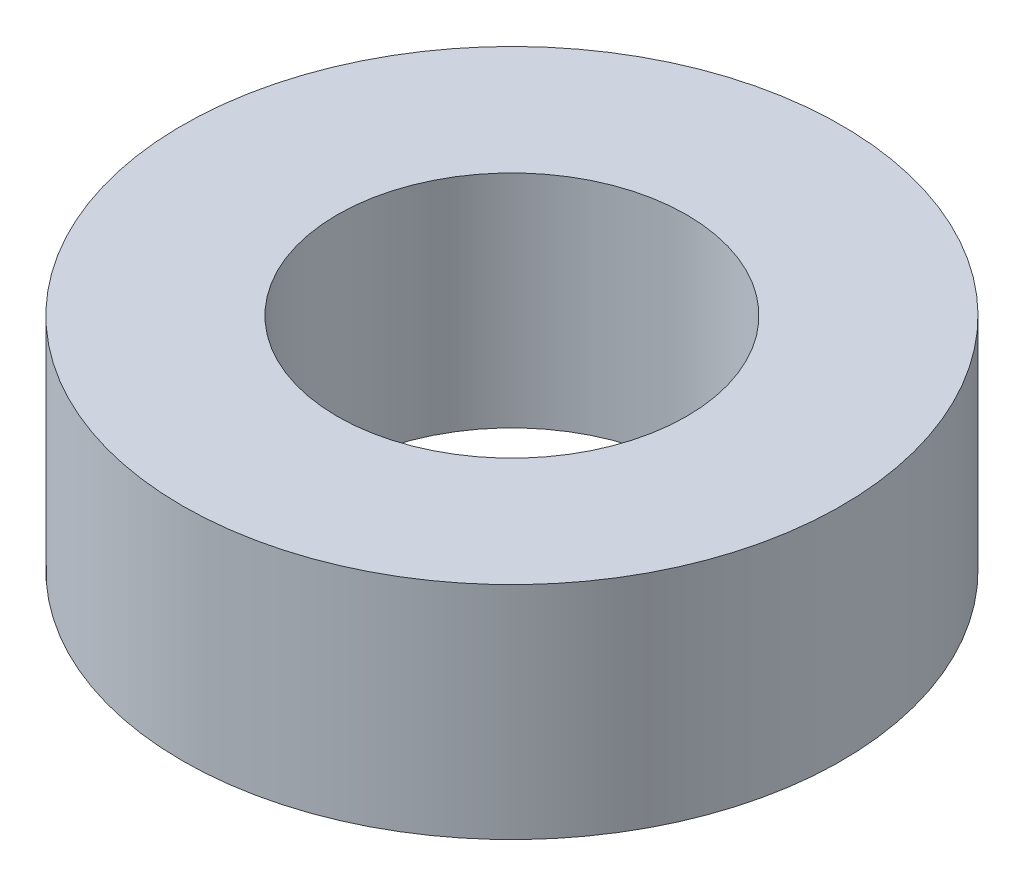
SolidWorks part; units mm, degrees
ref_plane "Front Plane" through (0, 0, 0) normal (0, 0, 1) x (1, 0, 0)
ref_plane "Top Plane" through (0, 0, 0) normal (0, 1, 0) x (1, 0, 0)
ref_plane "Right Plane" through (0, 0, 0) normal (1, 0, 0) x (0, 0, -1)
sketch "Sketch1" plane through (0, 0, 0) normal (0, 1, 0) x (1, 0, 0)
  circle A0 centre (0, 0) radius 5
  circle A1 centre (0, 0) radius 2.65
  dimension "D1" = 10
  dimension "D2" = 5.3
extrude "Boss-Extrude1" add sketch "Sketch1" along normal blind 3.35
